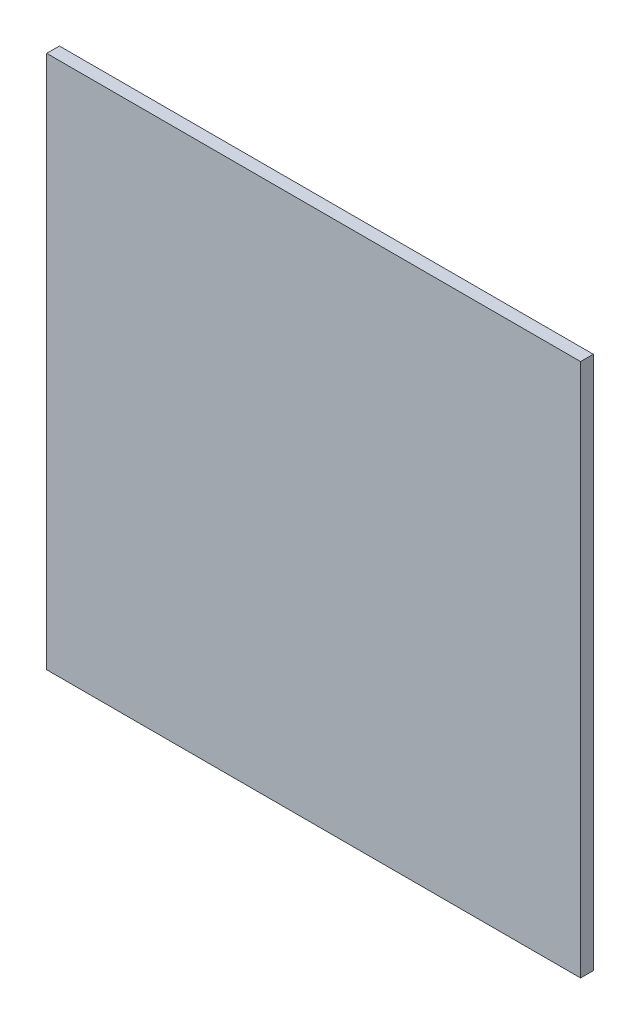
SolidWorks part; units mm, degrees
material "PC High Viscosity"
ref_plane "Front Plane" through (0, 0, 0) normal (0, 0, 1) x (1, 0, 0)
ref_plane "Top Plane" through (0, 0, 0) normal (0, 1, 0) x (1, 0, 0)
ref_plane "Right Plane" through (0, 0, 0) normal (1, 0, 0) x (0, 0, -1)
sketch "Sketch1" plane through (0, 0, 0) normal (0, 0, 1) x (1, 0, 0)
  line L1 (-133.35, -133.35) -> (133.35, -133.35)
  line L2 (-133.35, -133.35) -> (-133.35, 133.35)
  line L3 (-133.35, 133.35) -> (133.35, 133.35)
  line L4 (133.35, -133.35) -> (133.35, 133.35)
  line L5 (-133.35, -133.35) -> (133.35, 133.35) construction
  line L6 (-133.35, 133.35) -> (133.35, -133.35) construction
  point P0 (0, 0)
  dimension "D1" = 266.7
extrude "Boss-Extrude1" add sketch "Sketch1" along normal blind 6.35
hole_wizard "1/4 Clearance Hole1" [suppressed] positions "Sketch2" profile "Sketch3" hole size "1/4" standard "ANSI Inch"
sketch "Sketch2" plane through (0, 0, 6.35) normal (0, 0, 1) x (1, 0, 0)
  line L0 (0, 133.35) -> (0, -133.35) construction
  line L1 (133.35, 133.35) -> (-133.35, 133.35) construction
  line L2 (-133.35, -133.35) -> (133.35, -133.35) construction
  line L3 (-133.35, 0) -> (133.35, 0) construction
  line L4 (-133.35, 133.35) -> (-133.35, -133.35) construction
  line L5 (133.35, -133.35) -> (133.35, 133.35) construction
  line L7 (-103.1875, -103.1875) -> (103.1875, -103.1875) construction
  line L8 (-103.1875, -103.1875) -> (-103.1875, 103.1875) construction
  line L9 (-103.1875, 103.1875) -> (103.1875, 103.1875) construction
  line L10 (103.1875, -103.1875) -> (103.1875, 103.1875) construction
  line L11 (-103.1875, -103.1875) -> (103.1875, 103.1875) construction
  line L12 (-103.1875, 103.1875) -> (103.1875, -103.1875) construction
  line L13 (-133.35, 104.775) -> (-117.475, 104.775) construction
  line L16 (-104.775, 117.475) -> (-104.775, 133.35) construction
  arc A0 (-117.475, 104.775) -> (-104.775, 117.475) centre (-117.475, 117.475) ccw construction
  point P0 (-117.475, 117.475)
  point P17 (-117.475, -117.475)
  point P19 (117.475, -117.475)
  point P20 (117.475, 117.475)
  point P145 (0, 0)
  dimension "D4" = 12.7
  dimension "D1" = 15.875
  dimension "D2" = 15.875
  dimension "D3" = 206.375
sketch "Sketch3" plane through (-117.475, 117.475, 6.35) normal (1, 0, 0) x (0, -1, 0)
  line L0 (0, 0) -> (0, 6.35)
  line L1 (0, 6.35) -> (3.3782, 6.35)
  line L2 (3.3782, 6.35) -> (3.3782, 0)
  line L5 (3.3782, 0) -> (0, 0)
  line L11 (0, -6.35) -> (0, 107.95) construction
  dimension "Thru Hole Dia." = 6.7564
  dimension "Thru Hole Depth" = 6.35
fillet "Fillet1" [suppressed] radius 6.35
sketch "Sketch4" plane through (0, 0, 6.35) normal (0, 0, 1) x (1, 0, 0)
  line L0 (133.35, 133.35) -> (-133.35, 133.35) construction
  circle A0 centre (0, 133.35) radius 3.302
  dimension "D1" = 6.604
extrude "Cut-Extrude1" [suppressed] cut sketch "Sketch4" against normal through all
fillet "Fillet2" [suppressed] radius 1.5875
